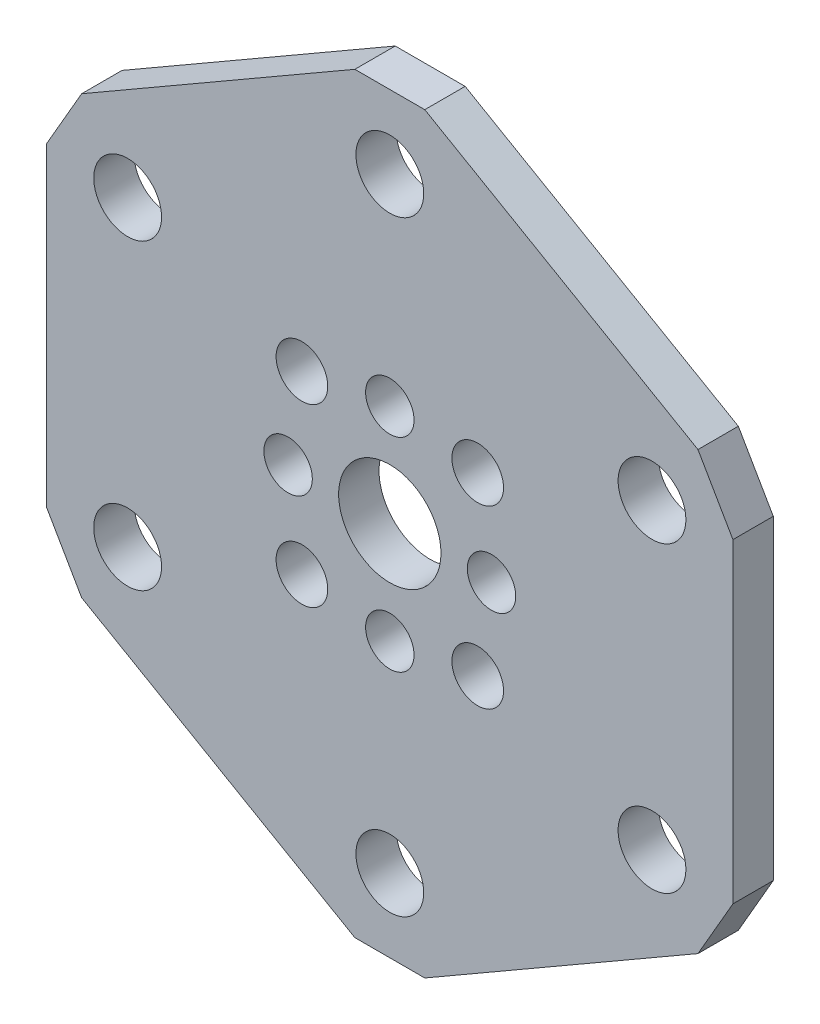
SolidWorks part; units mm, degrees
material "5052-H34"
ref_plane "Front Plane" through (0, 0, 0) normal (0, 0, 1) x (1, 0, 0)
ref_plane "Top Plane" through (0, 0, 0) normal (0, 1, 0) x (1, 0, 0)
ref_plane "Right Plane" through (0, 0, 0) normal (1, 0, 0) x (0, 0, -1)
ref_plane "Plane1" through (0, 0, 0) normal (0, 0, -1) x (-1, 0, 0)
sketch "Sketch1" plane through (0, 0, 0) normal (0, 0, -1) x (-1, 0, 0)
  line L0 (2.7496, 29.575) -> (-2.7496, 29.575)
  line L1 (-2.7496, 29.575) -> (-24.2379, 17.1687)
  line L2 (-24.2379, 17.1687) -> (-26.9875, 12.4062)
  line L3 (-26.9875, 12.4062) -> (-26.9875, -12.4062)
  line L4 (-26.9875, -12.4062) -> (-24.2379, -17.1687)
  line L5 (-24.2379, -17.1687) -> (-2.7496, -29.575)
  line L6 (-2.7496, -29.575) -> (2.7496, -29.575)
  line L7 (2.7496, -29.575) -> (24.2379, -17.1687)
  line L8 (24.2379, -17.1687) -> (26.9875, -12.4062)
  line L9 (26.9875, -12.4062) -> (26.9875, 12.4062)
  line L10 (26.9875, 12.4062) -> (24.2379, 17.1687)
  line L11 (24.2379, 17.1687) -> (2.7496, 29.575)
  circle A0 centre (20.6222, 11.9063) radius 2.667
  circle A1 centre (0, -23.8125) radius 2.667
  circle A2 centre (-20.6222, 11.9062) radius 2.667
  circle A3 centre (0, -8) radius 1.905
  circle A4 centre (0, 8) radius 1.905
  circle A5 centre (0, 23.8125) radius 2.667
  circle A6 centre (0, 0) radius 4.025
  circle A7 centre (-8, 0) radius 1.905
  circle A8 centre (8, 0) radius 1.905
  circle A9 centre (-20.6222, -11.9063) radius 2.667
  circle A10 centre (20.6222, -11.9063) radius 2.667
  circle A11 centre (-6.9148, 6.9148) radius 2.032
  circle A12 centre (-6.9148, -6.9148) radius 2.032
  circle A13 centre (6.9148, -6.9148) radius 2.032
  circle A14 centre (6.9148, 6.9148) radius 2.032
extrude "Boss-Extrude1" add sketch "Sketch1" against normal blind 3.175
